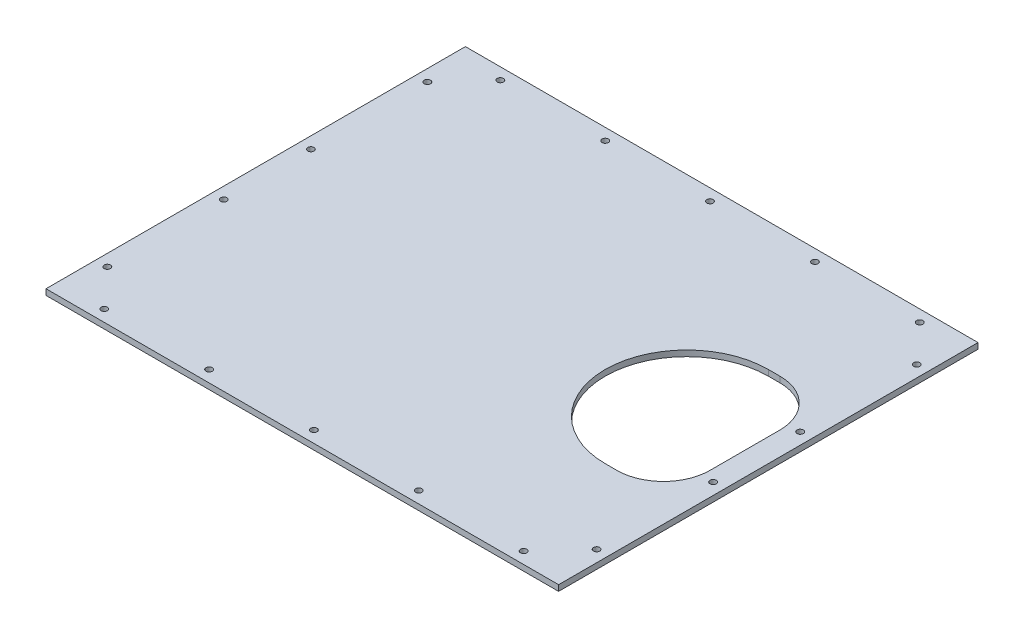
SolidWorks part; units mm, degrees
ref_plane "Plan de face" through (0, 0, 0) normal (0, 0, 1) x (1, 0, 0)
ref_plane "Plan de dessus" through (0, 0, 0) normal (0, 1, 0) x (1, 0, 0)
ref_plane "Plan de droite" through (0, 0, 0) normal (1, 0, 0) x (0, 0, -1)
sketch "Esquisse1" plane through (0, 0, 0) normal (0, 1, 0) x (1, 0, 0)
  line L0 (0, 180) -> (440, 180) construction
  line L1 (0, 0) -> (440, 0)
  line L2 (0, 0) -> (0, 360)
  line L3 (0, 360) -> (440, 360)
  line L4 (440, 0) -> (440, 360)
  line L5 (10, 350) -> (430, 350) construction
  line L6 (430, 10) -> (430, 350) construction
  line L7 (10, 10) -> (430, 10) construction
  line L8 (10, 10) -> (10, 350) construction
  line L9 (20, 340) -> (420, 340) construction
  line L10 (420, 20) -> (420, 340) construction
  line L11 (20, 20) -> (420, 20) construction
  line L12 (20, 20) -> (20, 340) construction
  line L13 (370, 250) -> (420, 250)
  line L14 (420, 250) -> (420, 110)
  line L15 (420, 110) -> (370, 110)
  line L16 (220, 360) -> (220, 0) construction
  arc A0 (370, 250) -> (370, 110) centre (370, 180) ccw
  circle A1 centre (40, 350) radius 2.7
  circle A2 centre (130, 350) radius 2.7
  circle A3 centre (220, 350) radius 2.7
  circle A4 centre (310, 350) radius 2.7
  circle A5 centre (400, 350) radius 2.7
  circle A6 centre (400, 10) radius 2.7
  circle A7 centre (310, 10) radius 2.7
  circle A8 centre (220, 10) radius 2.7
  circle A9 centre (130, 10) radius 2.7
  circle A10 centre (40, 10) radius 2.7
  circle A11 centre (10, 217.3673) radius 2.7
  circle A12 centre (10, 317.3673) radius 2.7
  circle A13 centre (10, 42.6327) radius 2.7
  circle A14 centre (10, 142.6327) radius 2.7
  circle A15 centre (430, 142.6327) radius 2.7
  circle A16 centre (430, 42.6327) radius 2.7
  circle A17 centre (430, 317.3673) radius 2.7
  circle A18 centre (430, 217.3673) radius 2.7
  dimension "D6" = 5.4
  dimension "D9" = 5.4
  dimension "D1" = 360
  dimension "D2" = 440
  dimension "D5" = 50
  dimension "D7" = 40
  dimension "D10" = 37.3673
  dimension "D3" = 10
  dimension "D4" = 10
  dimension "D8" = 5
  dimension "D11" = 2
extrude "Boss.-Extru.1" add sketch "Esquisse1" along normal blind 5
fillet "Congé1" radius 40 2 edges at (420, 2.5, -110) (420, 2.5, -250)
